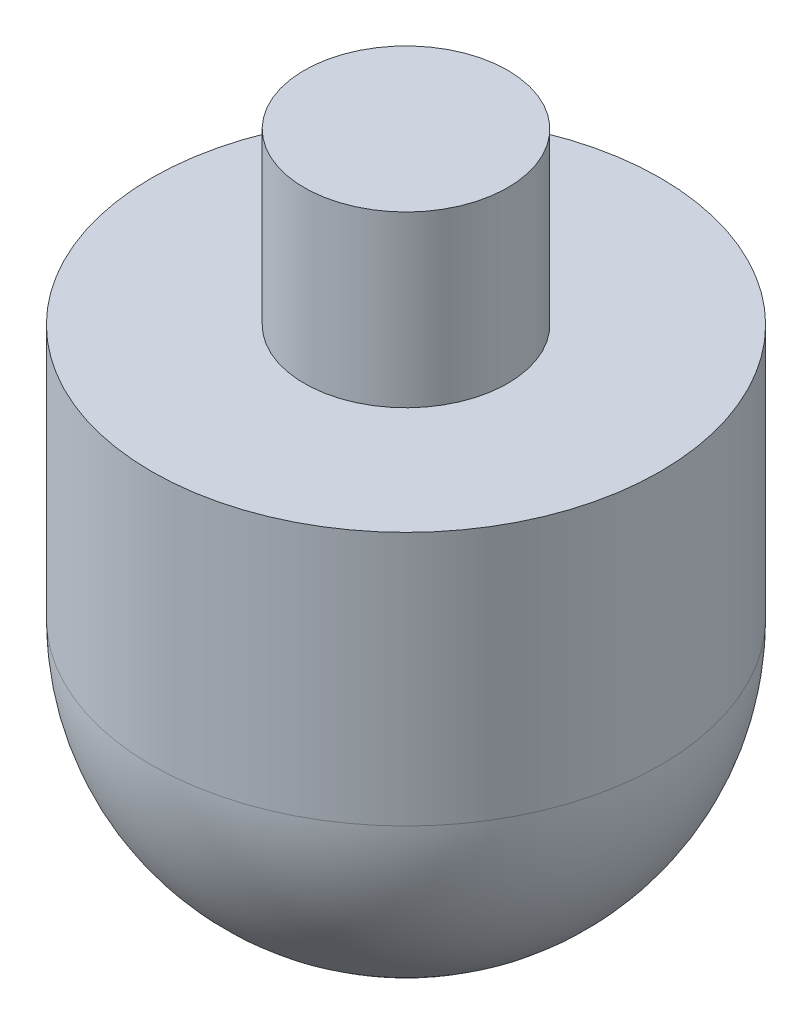
SolidWorks part; units mm, degrees
ref_plane "Front Plane" through (0, 0, 0) normal (0, 0, 1) x (1, 0, 0)
ref_plane "Top Plane" through (0, 0, 0) normal (0, 1, 0) x (1, 0, 0)
ref_plane "Right Plane" through (0, 0, 0) normal (1, 0, 0) x (0, 0, -1)
sketch "Sketch1" plane through (0, 0, 0) normal (0, 0, 1) x (1, 0, 0)
  line L0 (0, 0) -> (0, 50.2473) construction
  line L1 (0, 0) -> (15, 0)
  line L2 (15, 0) -> (15, 30)
  line L3 (15, 30) -> (6, 30)
  line L4 (6, 30) -> (6, 40)
  line L5 (6, 40) -> (0, 40)
  line L6 (0, 40) -> (0, 0)
  dimension "D1" = 30
  dimension "D2" = 12
  dimension "D3" = 10
  dimension "D4" = 40
revolve "Revolve1" add sketch "Sketch1" angle 360 about L0
fillet "Fillet2" radius 15 1 edges at (0, 0, -15)
